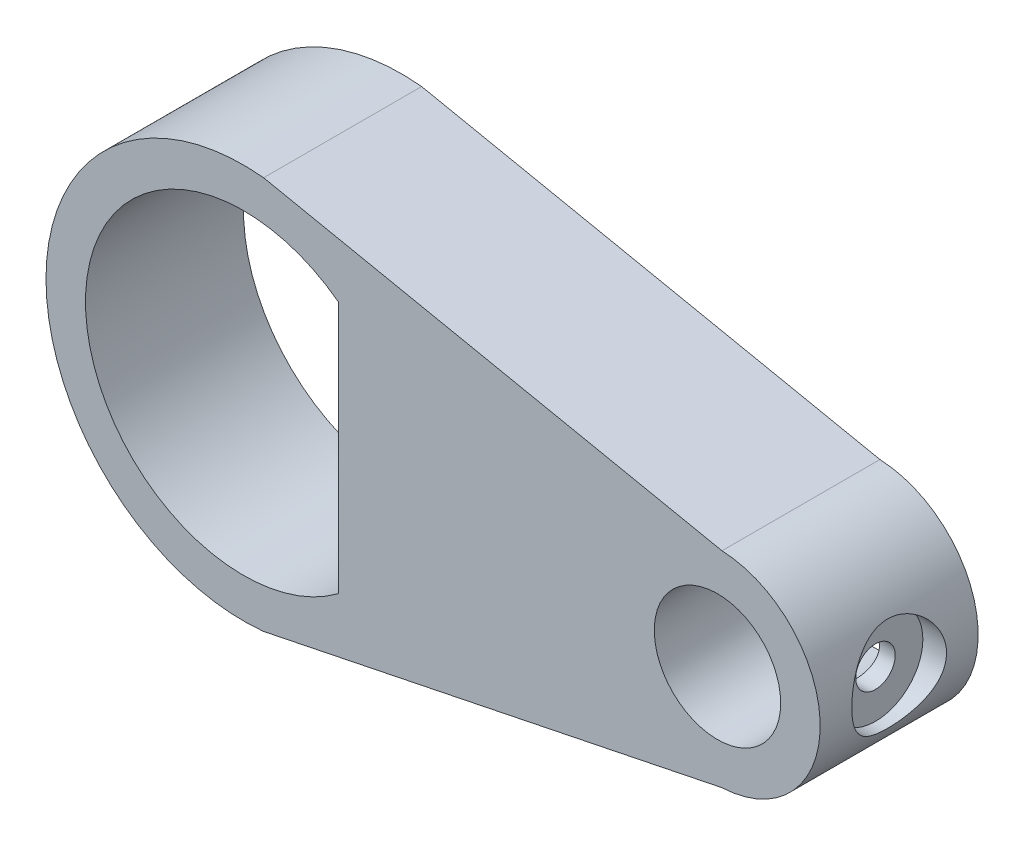
SolidWorks part; units mm, degrees
ref_plane "Front Plane" through (0, 0, 0) normal (0, 0, 1) x (1, 0, 0)
ref_plane "Top Plane" through (0, 0, 0) normal (0, 1, 0) x (1, 0, 0)
ref_plane "Right Plane" through (0, 0, 0) normal (1, 0, 0) x (0, 0, -1)
sketch "Sketch1" plane through (0, 0, 0) normal (0, 0, 1) x (1, 0, 0)
  line L0 (-15, 0) -> (15, 0) construction
  line L1 (15.2836, 6.4938) -> (-13.727, 12.435)
  line L2 (15.2836, -6.4938) -> (-13.727, -12.435)
  line L7 (-9, -8) -> (-9, 8)
  arc A2 (-13.727, 12.435) -> (-13.727, -12.435) centre (-15, 0) ccw
  arc A3 (15.2836, -6.4938) -> (15.2836, 6.4938) centre (15, 0) ccw
  circle A5 centre (15, 0) radius 4
  arc A6 (-9, 8) -> (-9, -8) centre (-15, 0) ccw
  point P4 (0, 0)
  point P10 (-15, 6)
  point P17 (-15, 6)
  point P18 (-9, 0)
extrude "Boss-Extrude1" add sketch "Sketch1" along normal blind 10
ref_plane "Plane1" through (22, 0, 0) normal (1, 0, 0) x (0, 0, -1)
sketch "Sketch2" plane through (22, 0, 0) normal (1, 0, 0) x (0, 0, -1)
  line L0 (0, 0) -> (-10, 0)
  line L1 (-10, 6.4938) -> (-10, -6.4938) construction
  circle A0 centre (-5, 0) radius 1.25
extrude "Cut-Extrude1" cut sketch "Sketch2" against normal blind 7 contours L0 A0 | L0 A0
sketch "Sketch3" plane through (22, 0, 0) normal (1, 0, 0) x (0, 0, -1)
  circle A0 centre (-5, 0) radius 3
extrude "Cut-Extrude2" cut sketch "Sketch3" against normal blind 2
